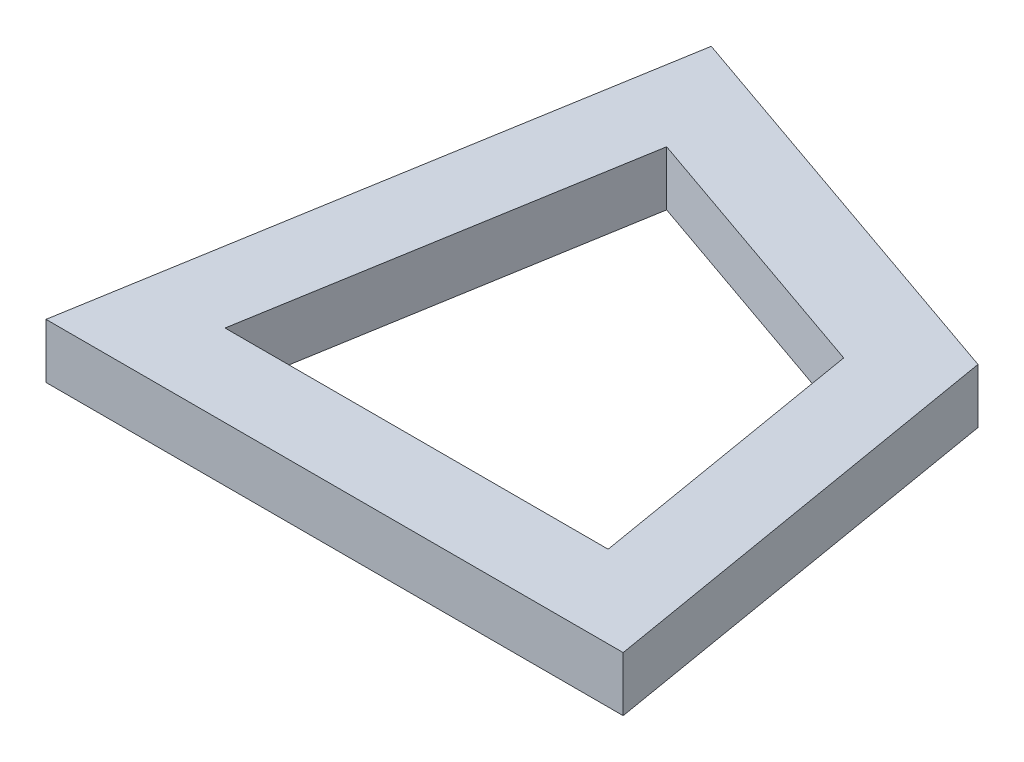
SolidWorks part; units mm, degrees
ref_plane "Front Plane" through (0, 0, 0) normal (0, 0, 1) x (1, 0, 0)
ref_plane "Top Plane" through (0, 0, 0) normal (0, 1, 0) x (1, 0, 0)
ref_plane "Right Plane" through (0, 0, 0) normal (1, 0, 0) x (0, 0, -1)
sketch "Sketch1" plane through (0, 0, 0) normal (0, 1, 0) x (1, 0, 0)
  line L0 (0, 0) -> (21.1142, 0)
  line L1 (21.1142, 0) -> (18.4752, 15.6194)
  line L2 (18.4752, 15.6194) -> (3.5176, 20.8191)
  line L3 (3.5176, 20.8191) -> (0, 0)
  line L4 (5.8844, 16.8202) -> (3.5494, 3)
  line L5 (3.5494, 3) -> (17.5648, 3)
  line L6 (17.5648, 3) -> (15.8129, 13.3688)
  line L7 (15.8129, 13.3688) -> (5.8844, 16.8202)
  point P4 (0, 0)
  point P10 (35.273, 13.2401)
  point P11 (27.7587, 61.9651)
  point P12 (35.2745, 13.2436)
  point P13 (30.6569, 10.5612)
  point P14 (35.2745, 13.2436)
  point P15 (32.8598, 27.5353)
  dimension "D1" = 21.1142
  dimension "D2" = 80.421
  dimension "D3" = 80.41
  dimension "D4" = 80.41
  dimension "D6" = 15.8408
  dimension "D7" = 15.8357
  dimension "D8" = 21.1142
  dimension "D5" = 3
extrude "Boss-Extrude1" add sketch "Sketch1" along normal blind 2
